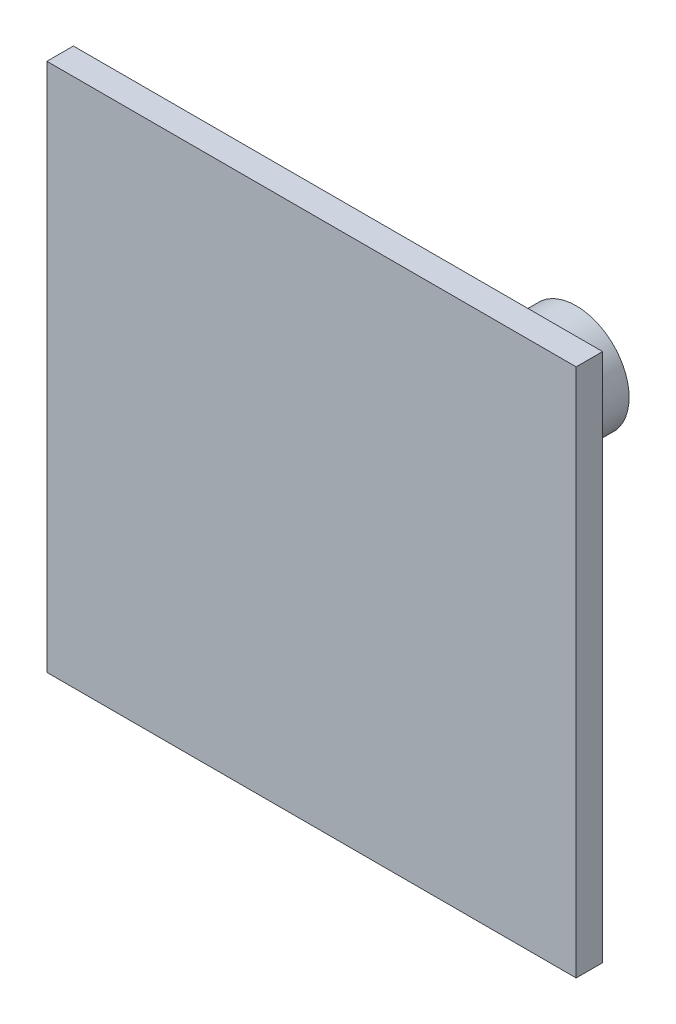
SolidWorks part; units mm, degrees
ref_plane "Front Plane" through (0, 0, 0) normal (0, 0, 1) x (1, 0, 0)
ref_plane "Top Plane" through (0, 0, 0) normal (0, 1, 0) x (1, 0, 0)
ref_plane "Right Plane" through (0, 0, 0) normal (1, 0, 0) x (0, 0, -1)
sketch "Sketch1" plane through (0, 0, 0) normal (0, 0, 1) x (1, 0, 0)
  line L1 (-102.4259, 67.1159) -> (97.5741, 67.1159)
  line L2 (-102.4259, 67.1159) -> (-102.4259, -132.8841)
  line L3 (-102.4259, -132.8841) -> (97.5741, -132.8841)
  line L4 (97.5741, 67.1159) -> (97.5741, -132.8841)
  dimension "D1" = 200
  dimension "D2" = 200
extrude "Boss-Extrude1" add sketch "Sketch1" along normal blind 10
sketch "Sketch2" plane through (0, 0, 0) normal (0, 0, -1) x (-1, 0, 0)
  line L0 (-97.5741, 67.1159) -> (102.4259, -132.8841)
  line L1 (102.4259, -132.8841) -> (-97.5741, -132.8841) construction
  line L2 (102.4259, 67.1159) -> (102.4259, -132.8841) construction
  line L3 (102.4259, -132.8841) -> (102.4259, 67.1159)
  line L4 (102.4259, 67.1159) -> (-97.5741, -132.8841)
  circle A0 centre (2.4259, -32.8841) radius 20
extrude "Boss-Extrude2" add sketch "Sketch2" along normal blind 90 contours A0
